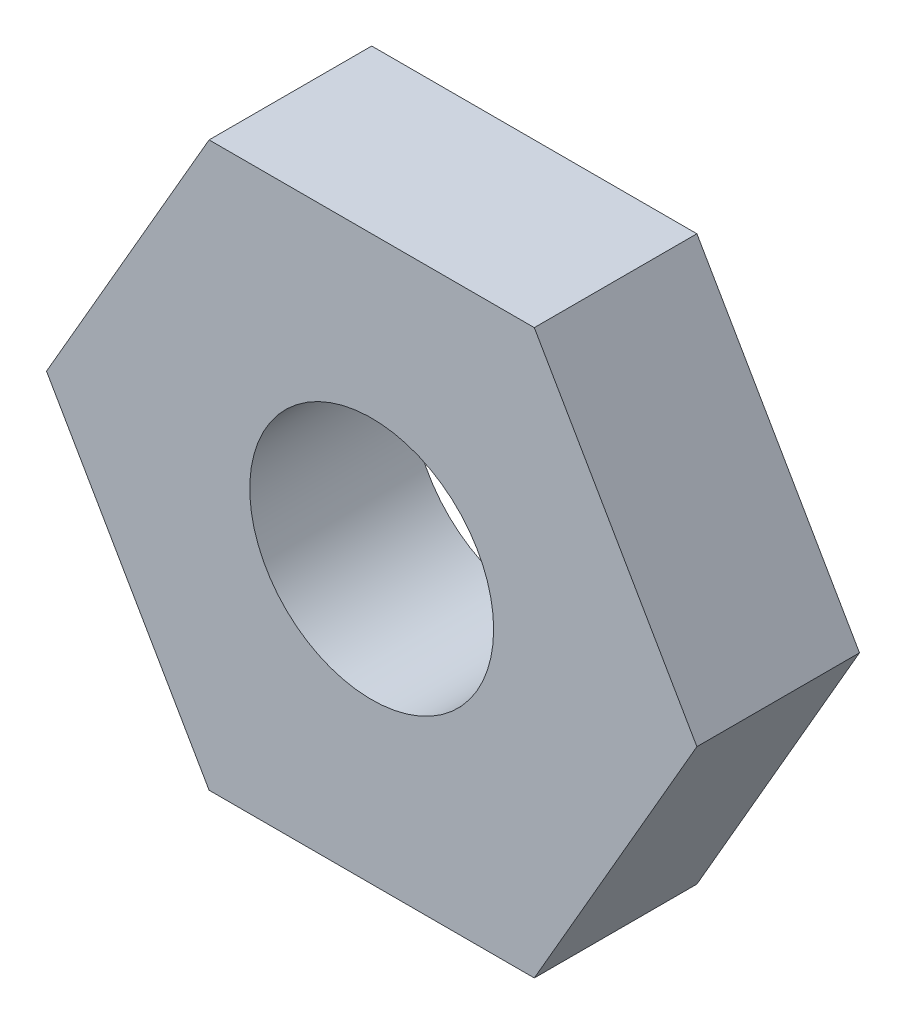
SolidWorks part; units mm, degrees
ref_plane "Plan de face" through (0, 0, 0) normal (0, 0, 1) x (1, 0, 0)
ref_plane "Plan de dessus" through (0, 0, 0) normal (0, 1, 0) x (1, 0, 0)
ref_plane "Plan de droite" through (0, 0, 0) normal (1, 0, 0) x (0, 0, -1)
sketch "Esquisse1" plane through (0, 0, 0) normal (0, 0, 1) x (1, 0, 0)
  line L0 (-4, 0) -> (-2, 3.4641)
  line L1 (-2, 3.4641) -> (2, 3.4641)
  line L2 (2, 3.4641) -> (4, 0)
  line L3 (4, 0) -> (2, -3.4641)
  line L4 (2, -3.4641) -> (-2, -3.4641)
  line L5 (-2, -3.4641) -> (-4, 0)
  line L6 (-4, 0) -> (0, 0) construction
  line L7 (0, 0) -> (4, 0) construction
  circle A0 centre (0, 0) radius 1.5
  dimension "D3" = 3
  dimension "D1" = 120
  dimension "D2" = 120
  dimension "D4" = 4
extrude "Boss.-Extru.1" add sketch "Esquisse1" along normal blind 2
